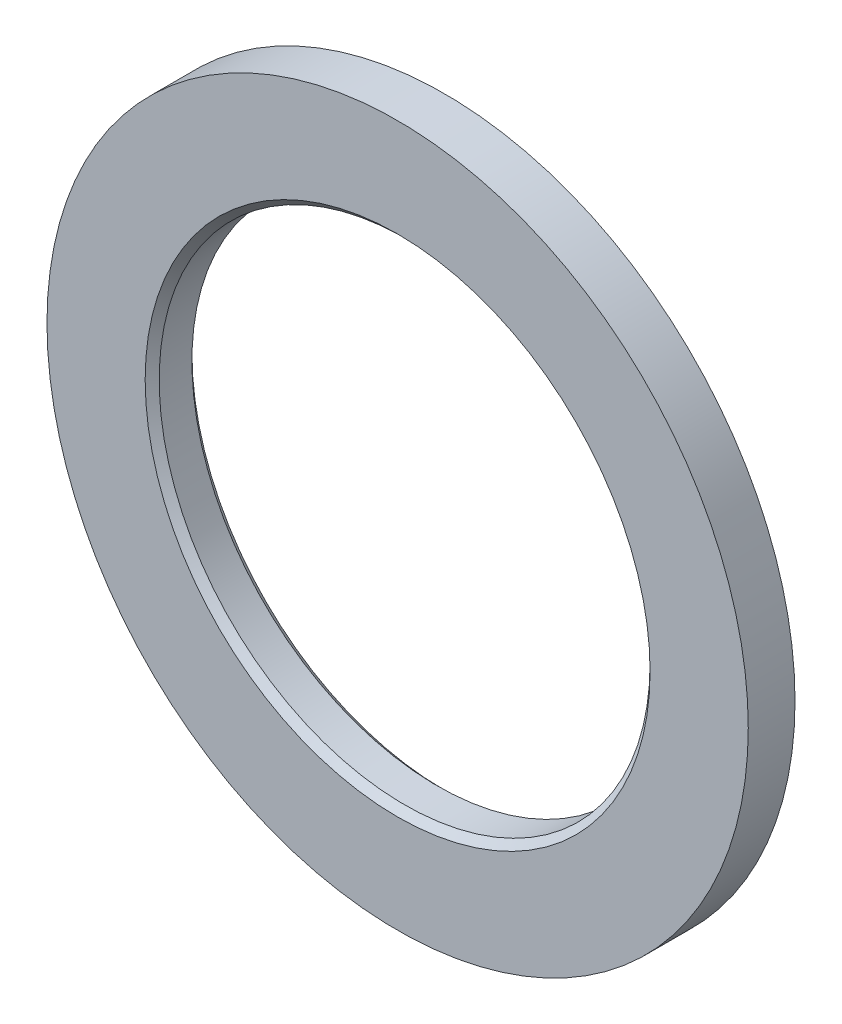
SolidWorks part; units mm, degrees
ref_plane "Front" through (0, 0, 0) normal (0, 0, 1) x (1, 0, 0)
ref_plane "Top" through (0, 0, 0) normal (0, 1, 0) x (1, 0, 0)
ref_plane "Right" through (0, 0, 0) normal (1, 0, 0) x (0, 0, -1)
sketch "Guard base" plane through (0, 0, 0) normal (0, 0, 1) x (1, 0, 0)
  circle A0 centre (0, 0) radius 37.5
  dimension "D1" = 75
extrude "Guard" add sketch "Guard base" along normal blind 5
sketch "Axle hole base" plane through (0, 0, 5) normal (0, 0, 1) x (1, 0, 0)
  circle A0 centre (0, 0) radius 26.25
  dimension "D1" = 52.5
extrude "Axle hole" cut sketch "Axle hole base" against normal through all
ref_axis "Center Z" through (0, 0, 0) along (0, 0, -1)
sketch "Mate ring room base" plane through (0, 0, 0) normal (0, 1, 0) x (1, 0, 0)
  line L0 (26.25, -5) -> (27, -5)
  line L1 (27, -5) -> (26.25, -4.25)
  line L2 (26.25, -4.25) -> (26.25, -5)
  line L5 (26.25, 0) -> (27, 0)
  line L6 (26.25, 0) -> (26.25, -0.75)
  line L7 (26.25, -0.75) -> (27, 0)
  dimension "D1" = 0.75
revolve "Mate ring room" cut sketch "Mate ring room base" angle 360 about axis through (0, 0, 0) along (0, 0, -1)
equation "\"mate_room\"= 0.25"
equation "\"removal_room\"= 0.75"
equation "\"large_inner_axle_diameter\"=20"
equation "\"D1@Axle hole base\"=\"53_55_spool_inner_diameter\"-\"spool_inner_diameter_room\"+\"mate_room\"*2"
equation "\"guard_thickness\"=5"
equation "\"spool_inner_diameter_room\"=1"
equation "\"D1@Guard\"=\"guard_thickness\""
equation "\"32_92_guard_diameter\"=50"
equation "\"D1@Guard base\"=\"53_55_guard_diameter\""
equation "\"32_92_spool_inner_diameter\"=32"
equation "\"32_92_spool_thickness\"=92"
equation "\"D1@Mate ring room base\" = \"removal_room\""
equation "\"bend_room_length_multiplier\"=3"
equation "\"small_inner_axle_diameter\"=17"
equation "\"32_92_extra_spool_thickness\"=-5"
equation "\"39_92_spool_inner_diameter\"=39"
equation "\"39_92_spool_thickness\"=92"
equation "\"39_92_guard_diameter\"=60"
equation "\"53_55_spool_inner_diameter\"=53"
equation "\"53_55_spool_thickness\"=55"
equation "\"53_55_guard_diameter\"=75"
